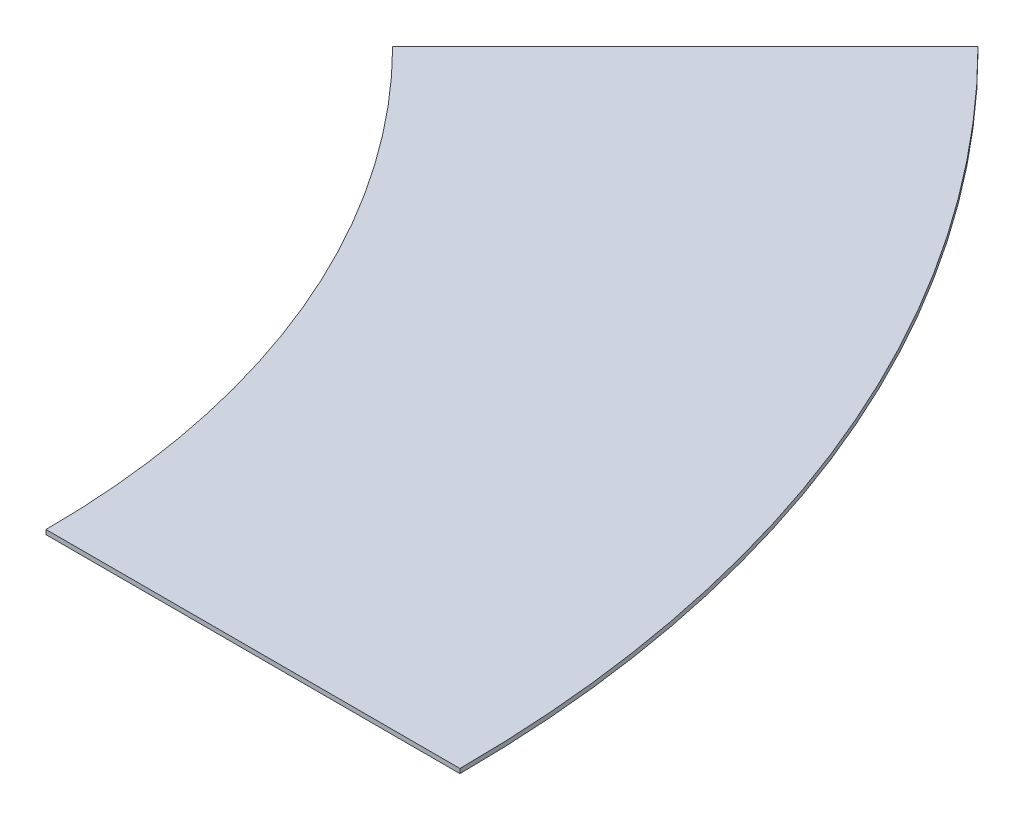
SolidWorks part; units mm, degrees
material "PE High Density"
ref_plane "Front Plane" through (0, 0, 0) normal (0, 0, 1) x (1, 0, 0)
ref_plane "Top Plane" through (0, 0, 0) normal (0, 1, 0) x (1, 0, 0)
ref_plane "Right Plane" through (0, 0, 0) normal (1, 0, 0) x (0, 0, -1)
sketch "Sketch2" plane through (0, 0, 0) normal (0, 0, 1) x (1, 0, 0)
  line L0 (0, 0) -> (0, 22.7316) construction
  line L1 (0, 0) -> (930, 0)
  line L2 (930, 2.5) -> (930, -2.5)
  line L3 (930, 2.5) -> (1390, 2.5)
  line L4 (1390, 2.5) -> (1390, -2.5)
  line L5 (1390, -2.5) -> (930, -2.5)
  point P7 (930, 0)
revolve "Revolve1" add sketch "Sketch2" angle 45 about L0
